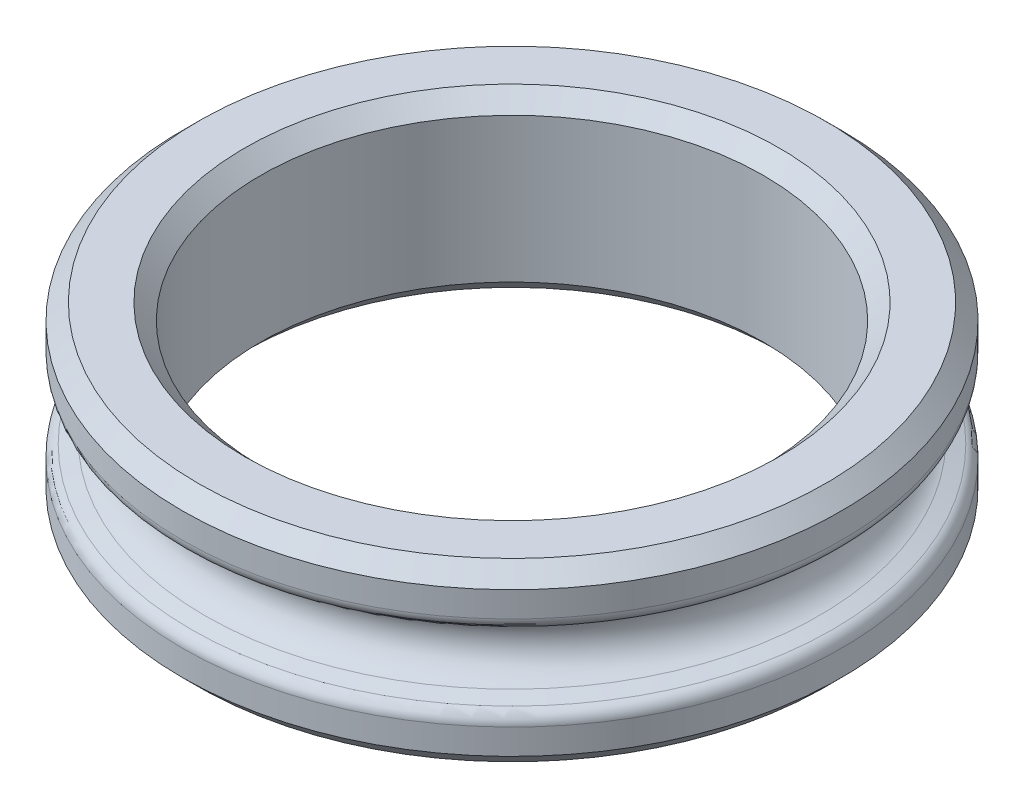
SolidWorks part; units mm, degrees
ref_plane "Front Plane" through (0, 0, 0) normal (0, 0, 1) x (1, 0, 0)
ref_plane "Top Plane" through (0, 0, 0) normal (0, 1, 0) x (1, 0, 0)
ref_plane "Right Plane" through (0, 0, 0) normal (1, 0, 0) x (0, 0, -1)
sketch "Sketch1" plane through (0, 0, 0) normal (0, 0, 1) x (1, 0, 0)
  line L0 (0, 0) -> (0, 4.6932) construction
  line L1 (0, 0) -> (3.9687, 0) construction
  line L2 (3.9688, 1.3891) -> (3.9688, -1.3891)
  line L3 (3.9688, -1.3891) -> (5, -1.3891)
  line L4 (5, -1.3891) -> (5, -0.5)
  line L6 (6.6554, 0) -> (3.9687, 0) construction
  line L7 (6.6554, 0) -> (-5, 0) construction
  line L8 (5, 1.3891) -> (5, 0.5)
  line L10 (3.9688, 1.3891) -> (5, 1.3891)
  line L11 (4.8413, 0.4742) -> (5.2, 0.5942)
  line L12 (5.2, 0.5942) -> (5.2, 1.3891)
  line L13 (5.2, 1.3891) -> (5, 1.3891)
  line L14 (5.2, -1.3891) -> (5, -1.3891)
  line L15 (5.2, -0.5942) -> (5.2, -1.3891)
  line L16 (4.8413, -0.4742) -> (5.2, -0.5942)
  arc A1 (5, 0.5) -> (5, -0.5) centre (5, 0) ccw
  dimension "D3" = 10
  dimension "D5" = 5
  dimension "D2" = 1
  dimension "D1" = 7.9375
  dimension "D4" = 2.7781
  dimension "D6" = 0
  dimension "D7" = 37
  dimension "D8" = 0.2
revolve "Revolve1" add sketch "Sketch1" angle 360 about L0
chamfer "Chamfer1" distance 0.25 angle 45 4 edges at (0, 1.3891, -3.9688) (0, 1.3891, -5.2) (0, -1.3891, -5.2) (0, -1.3891, -3.9688)
sketch "Sketch2" [suppressed] plane through (0, 0, 0) normal (0, 1, 0) x (1, 0, 0)
  circle A0 centre (0, 0) radius 5
sketch "Sketch3" [suppressed] plane through (0, 0, 0) normal (0, 1, 0) x (1, 0, 0)
  circle A0 centre (0, 0) radius 8
sketch "Sketch4" [suppressed] plane through (0, 0, 0) normal (0, 1, 0) x (1, 0, 0)
  circle A0 centre (0, 0) radius 11
sketch "Sketch5" [suppressed] plane through (0, 0, 0) normal (0, 1, 0) x (1, 0, 0)
  circle A0 centre (0, 0) radius 14
fillet "Fillet1" radius 0.2 2 edges at (0, 0.5942, -5.2) (0, -0.5942, -5.2)
fillet "Fillet2" [suppressed] radius 0.2
fillet "Fillet3" [suppressed] radius 0.2
fillet "Fillet4" [suppressed] radius 0.2
sketch "Sketch6" [suppressed] plane through (0, 1.3891, 0) normal (0, 1, 0) x (1, 0, 0)
  point P0 (0, 0)
